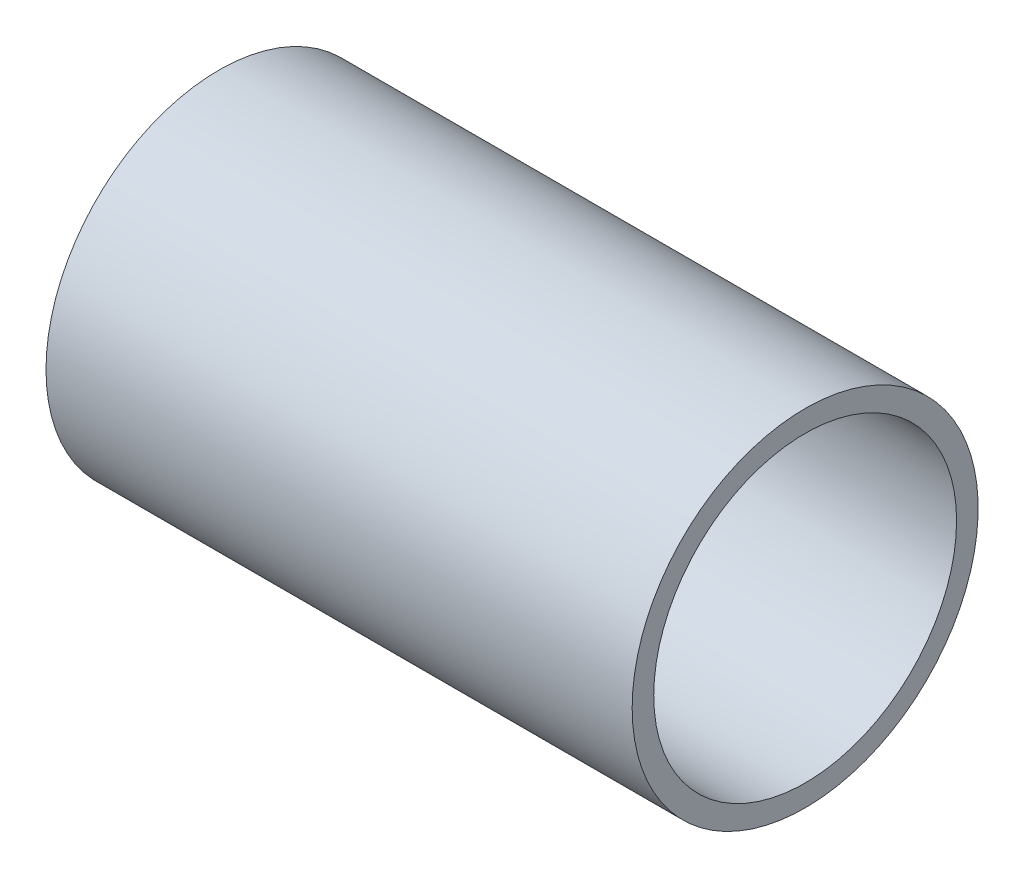
SolidWorks part; units mm, degrees
material "PE High Density"
ref_plane "Front Plane" through (0, 0, 0) normal (0, 0, 1) x (1, 0, 0)
ref_plane "Top Plane" through (0, 0, 0) normal (0, 1, 0) x (1, 0, 0)
ref_plane "Right Plane" through (0, 0, 0) normal (1, 0, 0) x (0, 0, -1)
sketch "Sketch2" plane through (0, 0, 0) normal (0, 0, 1) x (1, 0, 0)
  line L0 (0, 0) -> (74.8146, 0) construction
  line L2 (0, 141.732) -> (548.64, 141.732)
  line L3 (0, 141.732) -> (0, 161.925)
  line L4 (0, 161.925) -> (548.64, 161.925)
  line L5 (548.64, 141.732) -> (548.64, 161.925)
  dimension "D1" = 141.732
  dimension "D3" = 548.64
  dimension "D2" = 161.925
revolve "Revolve1" add sketch "Sketch2" angle 360 about L0
ref_plane "Midplane" through (274.32, 0, 0) normal (-1, 0, 0) x (0, 0, 1)
equation "\"ID\"= 11.160in"
equation "\"OD\"= 12.75in"
equation "\"Length\"= 21.6in"
equation "\"D1@Sketch2\"=\"ID\"/2"
equation "\"D3@Sketch2\"=\"Length\""
equation "\"D2@Sketch2\"=\"OD\"/2"
